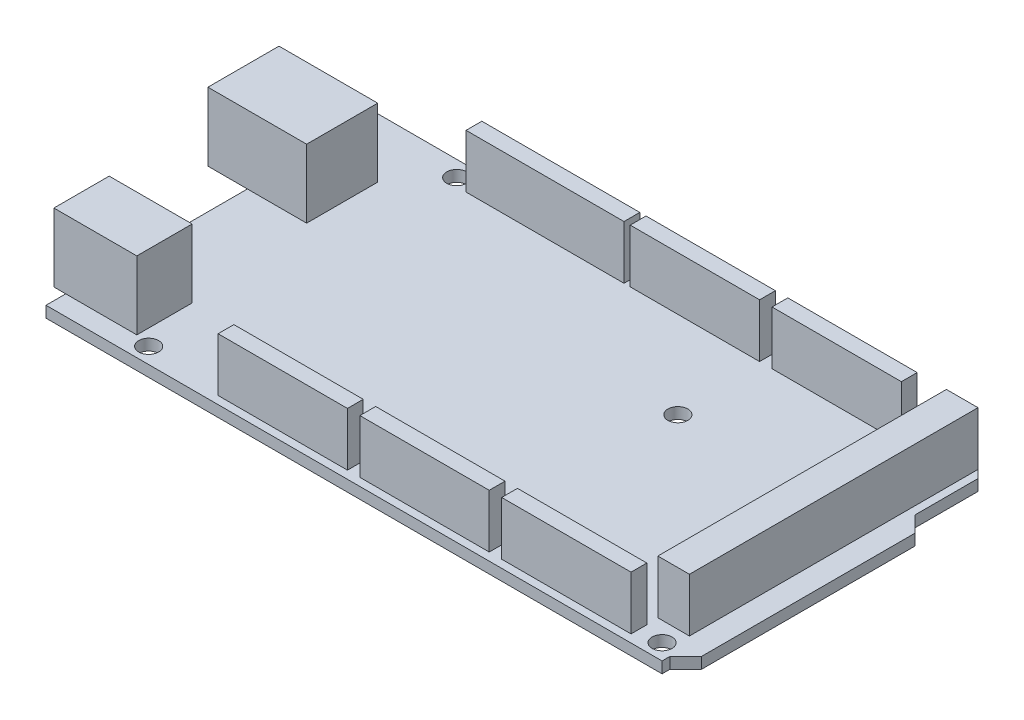
SolidWorks part; units mm, degrees
ref_plane "Front Plane" through (0, 0, 0) normal (0, 0, 1) x (1, 0, 0)
ref_plane "Top Plane" through (0, 0, 0) normal (0, 1, 0) x (1, 0, 0)
ref_plane "Right Plane" through (0, 0, 0) normal (1, 0, 0) x (0, 0, -1)
sketch "Sketch1" plane through (0, 0, 0) normal (0, 1, 0) x (1, 0, 0)
  line L0 (-49.53, -26.67) -> (49.53, -26.67)
  line L1 (49.53, -26.67) -> (49.53, -25.4)
  line L2 (49.53, -25.4) -> (52.07, -22.86)
  line L3 (52.07, -22.86) -> (52.07, 11.43)
  line L4 (52.07, 11.43) -> (49.53, 13.97)
  line L5 (49.53, 13.97) -> (49.53, 24.13)
  line L6 (49.53, 24.13) -> (46.99, 26.67)
  line L7 (46.99, 26.67) -> (-49.53, 26.67)
  line L8 (-49.53, 26.67) -> (-49.53, -26.67)
  line L9 (49.53, -26.67) -> (-49.53, 26.67) construction
  dimension "D1" = 53.34
  dimension "D2" = 101.6
  dimension "D3" = 99.06
  dimension "D4" = 1.27
  dimension "D5" = 2.54
  dimension "D6" = 96.52
  dimension "D7" = 34.29
extrude "Boss-Extrude1" add sketch "Sketch1" along normal blind 1.8
sketch "Sketch2" plane through (0, 1.8, 0) normal (0, 1, 0) x (1, 0, 0)
  line L0 (-49.53, -26.67) -> (49.53, -26.67) construction
  line L1 (-49.53, 26.67) -> (-49.53, -26.67) construction
  circle A0 centre (-35.56, -24.13) radius 1.6
  circle A1 centre (16.51, -19.05) radius 1.6
  circle A2 centre (16.51, 8.89) radius 1.6
  circle A3 centre (46.99, -24.13) radius 1.6
  circle A4 centre (40.64, 24.13) radius 1.6
  circle A5 centre (-34.29, 24.13) radius 1.6
  dimension "D1" = 3.2
  dimension "D2" = 2.54
  dimension "D3" = 13.97
  dimension "D4" = 1.27
  dimension "D5" = 5.08
  dimension "D6" = 50.8
  dimension "D7" = 27.94
  dimension "D8" = 15.24
  dimension "D9" = 24.13
  dimension "D10" = 96.52
extrude "Cut-Extrude1" cut sketch "Sketch2" against normal up to next
sketch "Sketch3" plane through (0, 1.8, 0) normal (0, 1, 0) x (1, 0, 0)
  line L0 (-49.53, 26.67) -> (-49.53, -26.67) construction
  line L1 (-40.005, 17.145) -> (-55.88, 17.145)
  line L2 (-40.005, 17.145) -> (-40.005, 5.715)
  line L3 (-40.005, 5.715) -> (-55.88, 5.715)
  line L4 (-55.88, 17.145) -> (-55.88, 5.715)
  line L5 (-49.53, -26.67) -> (49.53, -26.67) construction
  dimension "D1" = 11.43
  dimension "D2" = 15.875
  dimension "D3" = 6.35
  dimension "D4" = 32.385
extrude "Boss-Extrude2" add sketch "Sketch3" along normal blind 11
sketch "Sketch4" plane through (0, 1.8, 0) normal (0, 1, 0) x (1, 0, 0)
  line L0 (-51.435, -23.495) -> (-38.1, -23.495)
  line L1 (-51.435, -23.495) -> (-51.435, -14.605)
  line L2 (-51.435, -14.605) -> (-38.1, -14.605)
  line L3 (-38.1, -23.495) -> (-38.1, -14.605)
  line L4 (-49.53, 5.715) -> (-49.53, -26.67) construction
  line L5 (-49.53, -26.67) -> (49.53, -26.67) construction
  dimension "D1" = 8.89
  dimension "D2" = 13.335
  dimension "D3" = 1.905
  dimension "D4" = 3.175
extrude "Boss-Extrude3" add sketch "Sketch4" along normal blind 11
sketch "Sketch5" plane through (0, 1.8, 0) normal (0, 1, 0) x (1, 0, 0)
  line L0 (-49.53, -23.495) -> (-49.53, -26.67) construction
  line L1 (-23.13, -22.86) -> (-2.33, -22.86)
  line L2 (-23.13, -22.86) -> (-23.13, -25.4)
  line L3 (-23.13, -25.4) -> (-2.33, -25.4)
  line L4 (-2.33, -22.86) -> (-2.33, -25.4)
  line L5 (-0.33, -22.86) -> (20.47, -22.86)
  line L6 (-0.33, -22.86) -> (-0.33, -25.4)
  line L7 (-0.33, -25.4) -> (20.47, -25.4)
  line L8 (20.47, -22.86) -> (20.47, -25.4)
  line L9 (22.47, -22.86) -> (43.27, -22.86)
  line L10 (22.47, -22.86) -> (22.47, -25.4)
  line L11 (22.47, -25.4) -> (43.27, -25.4)
  line L12 (43.27, -22.86) -> (43.27, -25.4)
  line L13 (43.18, 25.4) -> (48.26, 25.4)
  line L14 (43.18, 25.4) -> (43.18, -21)
  line L15 (43.18, -21) -> (48.26, -21)
  line L16 (48.26, 25.4) -> (48.26, -21)
  line L17 (38.48, 25.4) -> (17.68, 25.4)
  line L18 (38.48, 25.4) -> (38.48, 22.86)
  line L19 (38.48, 22.86) -> (17.68, 22.86)
  line L20 (17.68, 25.4) -> (17.68, 22.86)
  line L21 (15.68, 25.4) -> (-5.12, 25.4)
  line L22 (15.68, 25.4) -> (15.68, 22.86)
  line L23 (15.68, 22.86) -> (-5.12, 22.86)
  line L24 (-5.12, 25.4) -> (-5.12, 22.86)
  line L25 (-6.12, 25.4) -> (-31.52, 25.4)
  line L26 (-6.12, 25.4) -> (-6.12, 22.86)
  line L27 (-6.12, 22.86) -> (-31.52, 22.86)
  line L28 (-31.52, 25.4) -> (-31.52, 22.86)
  line L31 (38.48, 24.13) -> (49.53, 24.13) construction
  line L32 (49.53, 13.97) -> (49.53, 24.13) construction
  line L33 (46.99, 26.67) -> (-49.53, 26.67) construction
  line L34 (-49.53, -26.67) -> (49.53, -26.67) construction
  point P30 (-23.13, -24.13)
  dimension "D1" = 2.54
  dimension "D2" = 20.8
  dimension "D3" = 26.4
  dimension "D4" = 2.54
  dimension "D5" = 2
  dimension "D6" = 2
  dimension "D7" = 5.08
  dimension "D8" = 46.4
  dimension "D9" = 1.27
  dimension "D10" = 2.54
  dimension "D11" = 1.27
  dimension "D12" = 4.7
  dimension "D13" = 2
  dimension "D14" = 1
  dimension "D15" = 25.4
extrude "Boss-Extrude4" add sketch "Sketch5" along normal blind 8.6
